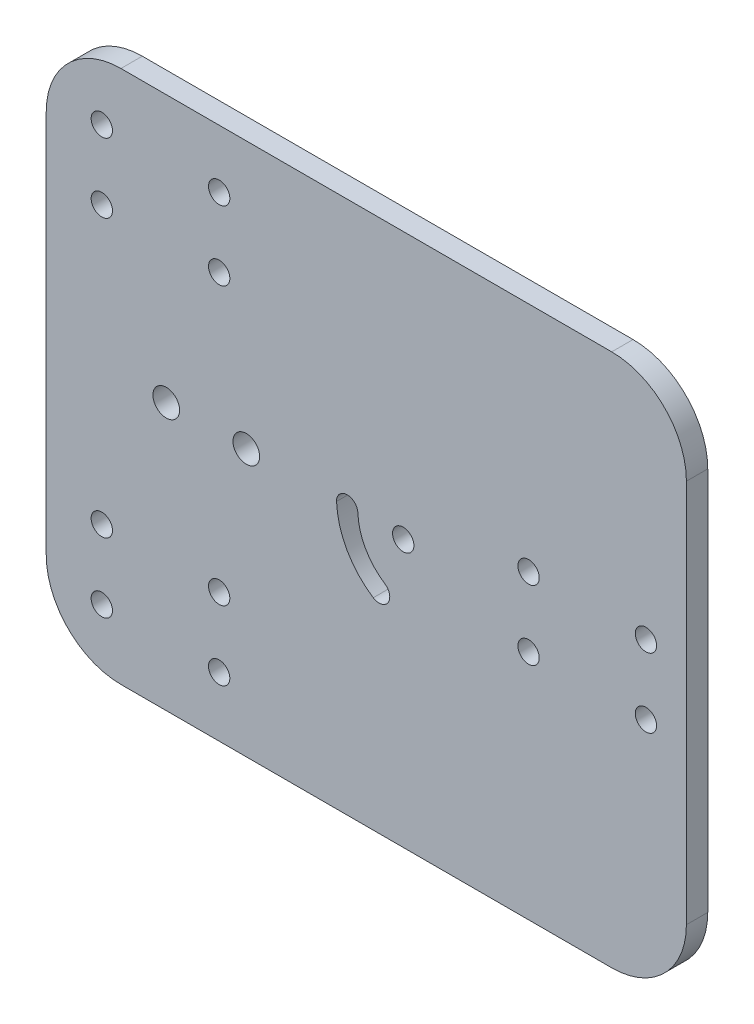
SolidWorks part; units mm, degrees
ref_plane "前视基准面" through (0, 0, 0) normal (0, 0, 1) x (1, 0, 0)
ref_plane "上视基准面" through (0, 0, 0) normal (0, 1, 0) x (1, 0, 0)
ref_plane "右视基准面" through (0, 0, 0) normal (1, 0, 0) x (0, 0, -1)
other "Configuration Table"
sketch "草图1" plane through (0, 0, 0) normal (0, 0, 1) x (1, 0, 0)
  line L1 (-52.6556, 38.8382) -> (67.3444, 38.8382)
  line L2 (-52.6556, 38.8382) -> (-52.6556, -61.1618)
  line L3 (-52.6556, -61.1618) -> (67.3444, -61.1618)
  line L4 (67.3444, 38.8382) -> (67.3444, -61.1618)
  dimension "D1" = 120
  dimension "D2" = 100
extrude "凸台-拉伸1" add sketch "草图1" along normal blind 4
fillet "圆角1" radius 14 4 edges at (67.3444, 38.8382, 2) (67.3444, -61.1618, 2) (-52.6556, -61.1618, 2) (-52.6556, 38.8382, 2)
sketch "草图2" plane through (0, 0, 4) normal (0, 0, 1) x (1, 0, 0)
  line L0 (-52.6556, 24.8382) -> (67.3444, 24.8382) construction
  line L1 (-38.6556, 38.8382) -> (-38.6556, -61.1618) construction
  line L2 (53.3444, -61.1618) -> (53.3444, 38.8382) construction
  line L3 (67.3444, -47.1618) -> (-52.6556, -47.1618) construction
  circle A0 centre (53.3444, 24.8382) radius 1.5
  circle A1 centre (-38.6556, 24.8382) radius 1.5
  circle A2 centre (-38.6556, -47.1618) radius 1.5
  circle A3 centre (53.3444, -47.1618) radius 1.5
  dimension "D1" = 3
extrude "切除-拉伸1" [suppressed] cut sketch "草图2" against normal through all
sketch "草图7" plane through (0, 0, 0) normal (0, 0, -1) x (-1, 0, 0)
  line L0 (-67.3444, -11.1618) -> (52.6556, -11.1618) construction
  line L1 (-67.3444, -47.1618) -> (-67.3444, 24.8382) construction
  line L2 (52.6556, 24.8382) -> (52.6556, -47.1618) construction
  circle A2 centre (15.1556, -11.1618) radius 2.5
  circle A3 centre (30.1556, -11.1618) radius 2.5
  point P12 (28.0161, -11.1618)
  point P15 (42.0015, -11.1618)
  point P16 (34.4709, -11.1618)
  point P18 (48.3219, -16.1216)
  point P19 (52.6556, -15.5837)
  dimension "D2" = 5
  dimension "D5" = 37.5
  dimension "D6" = 15
  dimension "D1" = 5
extrude "切除-拉伸2" cut sketch "草图7" against normal through all
sketch "草图14" plane through (0, 0, 0) normal (0, 0, -1) x (-1, 0, 0)
  line L0 (-67.3444, -11.1618) -> (52.6556, -11.1618) construction
  line L1 (-67.3444, -47.1618) -> (-67.3444, 24.8382) construction
  line L2 (52.6556, 24.8382) -> (52.6556, -47.1618) construction
  line L3 (-59.7591, -4.6618) -> (-59.7591, -17.6618) construction
  line L4 (-59.7591, -11.1618) -> (-59.7591, 37.2821) construction
  line L5 (42.2409, 27.9421) -> (42.2409, 38.3713) construction
  line L6 (42.2409, 38.3713) -> (42.2409, -60.6949) construction
  arc A0 (-53.3444, 38.8382) -> (-67.3444, 24.8382) centre (-53.3444, 24.8382) ccw construction
  arc A1 (52.6556, 24.8382) -> (38.6556, 38.8382) centre (38.6556, 24.8382) ccw construction
  arc A2 (38.6556, -61.1618) -> (52.6556, -47.1618) centre (38.6556, -47.1618) ccw construction
  arc A17 (-1.7605, -11.2365) -> (-5.7577, -11.0872) centre (-3.7591, -11.1618) ccw
  arc A18 (-10.8349, -20.0841) -> (-8.6409, -23.4287) centre (-9.7379, -21.7564) ccw
  arc A19 (-8.6409, -23.4287) -> (-1.7605, -11.2365) centre (-17.0126, -10.6667) ccw
  circle A20 centre (42.2409, -49.9653) radius 2
  circle A21 centre (20.2409, -49.9653) radius 2
  circle A22 centre (42.2409, -36.9653) radius 2
  circle A23 centre (20.2409, -36.9653) radius 2
  circle A24 centre (42.2409, 14.9421) radius 2
  circle A25 centre (42.2409, 27.9421) radius 2
  circle A26 centre (20.2409, 14.9421) radius 2
  circle A27 centre (20.2409, 27.9421) radius 2
  arc A28 (-10.8349, -20.0841) -> (-5.7577, -11.0872) centre (-17.0126, -10.6667) ccw
  circle A29 centre (-14.2591, -11.1618) radius 2
  circle A30 centre (-37.7591, -17.6618) radius 2
  circle A31 centre (-59.7591, -17.6618) radius 2
  circle A32 centre (-59.7591, -4.6618) radius 2
  circle A33 centre (-37.7591, -4.6618) radius 2
extrude "切除-拉伸3" cut sketch "草图14" against normal through all
